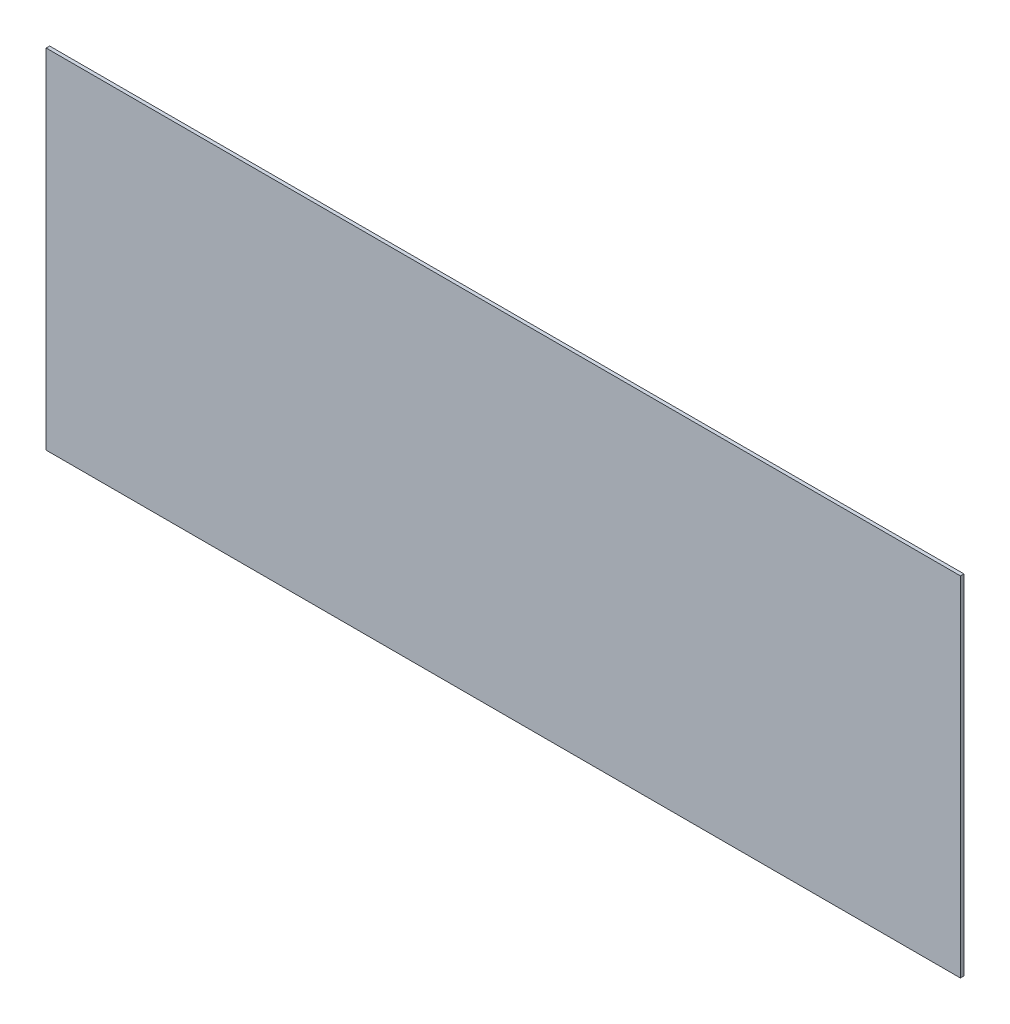
SolidWorks part; units mm, degrees
ref_plane "Front Plane" through (0, 0, 0) normal (0, 0, 1) x (1, 0, 0)
ref_plane "Top Plane" through (0, 0, 0) normal (0, 1, 0) x (1, 0, 0)
ref_plane "Right Plane" through (0, 0, 0) normal (1, 0, 0) x (0, 0, -1)
sketch "Sketch1" plane through (0, 0, 0) normal (0, 0, 1) x (1, 0, 0)
  line L1 (-33.3375, 12.7) -> (33.3375, 12.7)
  line L2 (-33.3375, 12.7) -> (-33.3375, -12.7)
  line L3 (-33.3375, -12.7) -> (33.3375, -12.7)
  line L4 (33.3375, 12.7) -> (33.3375, -12.7)
  line L5 (-33.3375, 12.7) -> (33.3375, -12.7) construction
  line L6 (-33.3375, -12.7) -> (33.3375, 12.7) construction
  point P0 (0, 0)
  dimension "D1" = 25.4
  dimension "D2" = 66.675
extrude "Boss-Extrude1" add sketch "Sketch1" along normal blind 0.254
